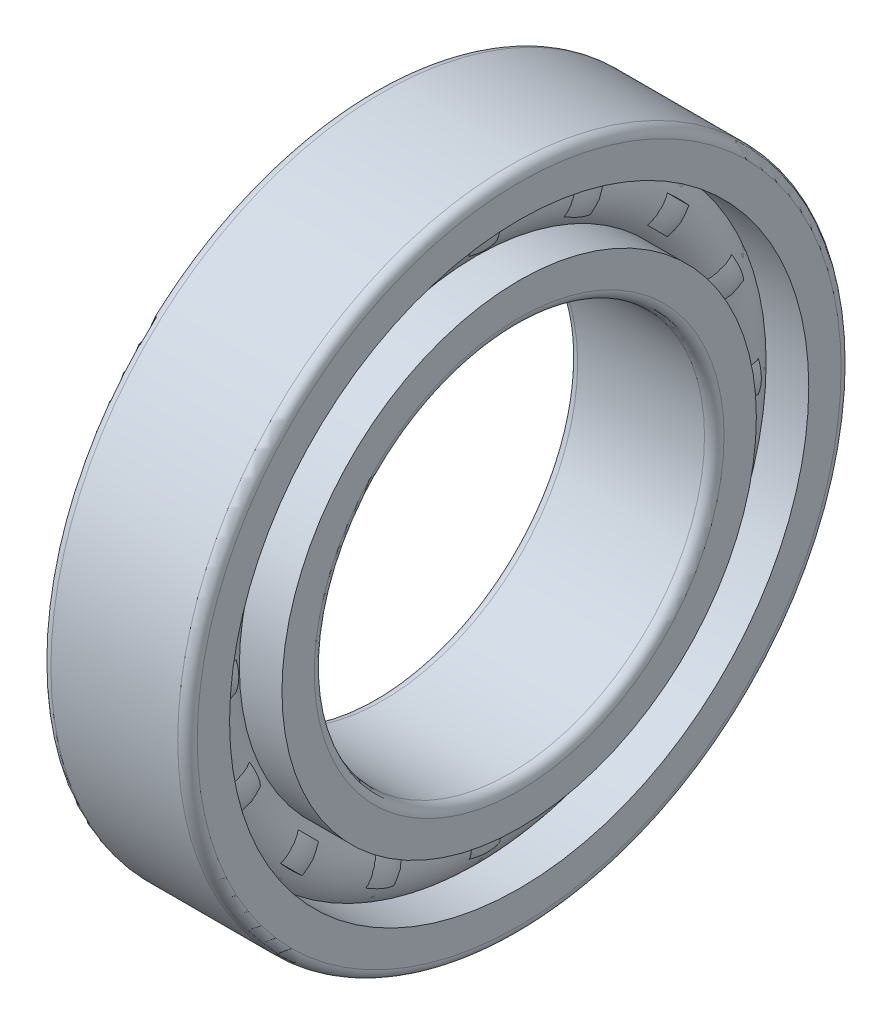
SolidWorks part; units mm, degrees
ref_plane "Přední rovina" through (0, 0, 0) normal (0, 0, 1) x (1, 0, 0)
ref_plane "Vrchní rovina" through (0, 0, 0) normal (0, 1, 0) x (1, 0, 0)
ref_plane "Pravá rovina" through (0, 0, 0) normal (1, 0, 0) x (0, 0, -1)
sketch "Skica1" plane through (0, 0, 0) normal (0, 0, 1) x (1, 0, 0)
  line L0 (0, 20) -> (0, 0) construction
  line L1 (-7.5, 34) -> (7.5, 34)
  line L2 (-7.5, 34) -> (-7.5, 20)
  line L3 (-7.5, 20) -> (7.5, 20)
  line L4 (7.5, 34) -> (7.5, 20)
  line L5 (0, 0) -> (7.5, 0) construction
  dimension "B" = 15
  dimension "d" = 40
  dimension "D_" = 68
sketch "Skica2" plane through (0, 0, 0) normal (0, 0, 1) x (1, 0, 0)
  line L0 (7.5, 34) -> (7.5, 20) construction
  line L1 (-7.5, 34) -> (7.5, 34)
  line L2 (-7.5, 34) -> (-7.5, 29.6859)
  line L3 (-7.5, 29.6859) -> (-3.1293, 29.6859)
  line L4 (7.5, 34) -> (7.5, 29.6859)
  line L5 (-7.5, 34) -> (-7.5, 20) construction
  line L6 (7.5, 20) -> (-7.5, 20)
  line L7 (7.5, 20) -> (7.5, 24.3141)
  line L8 (7.5, 24.3141) -> (3.1293, 24.3141)
  line L9 (-7.5, 20) -> (-7.5, 24.3141)
  line L10 (7.5, 29.6859) -> (4.1239, 27) construction
  line L11 (7.5, 29.6859) -> (-7.5, 24.3141) construction
  line L12 (0, 29.6859) -> (0, 31.1239) construction
  line L14 (3.1293, 29.6859) -> (7.5, 29.6859)
  line L15 (-3.1293, 24.3141) -> (-7.5, 24.3141)
  line L16 (0, 0) -> (-7.5, 0) construction
  line L17 (0, 27) -> (0, 22.8761) construction
  line L18 (0, 31.1239) -> (0, 32.562) construction
  line L19 (0, 32.562) -> (0, 34) construction
  circle A0 centre (0, 27) radius 4.1239 construction
  arc A1 (-3.1293, 29.6859) -> (3.1293, 29.6859) centre (0, 27) cw
  arc A2 (-3.1293, 24.3141) -> (3.1293, 24.3141) centre (0, 27) ccw
revolve "Otočit kolem osy1" add sketch "Skica2" angle 360 about L16
fillet "Zaoblit1" radius 1 2 edges at (7.5, 0, -34) (-7.5, 0, -34)
fillet "Zaoblit2" radius 1 2 edges at (7.5, 0, -20) (-7.5, 0, -20)
sketch "Skica3" plane through (0, 0, 0) normal (0, 0, 1) x (1, 0, 0)
  line L0 (0, 0) -> (7.5, 0) construction
  line L1 (7.5, -33) -> (7.5, 33) construction
  circle A0 centre (0, 27) radius 4.1239
  arc A1 (3.1293, 29.6859) -> (-3.1293, 29.6859) centre (0, 27) ccw construction
  circle A2 centre (0, 27) radius 4.1139
  dimension "D1" = 0.01
revolve "Otočit kolem osy2" add sketch "Skica3" angle 360 about L0
sketch "Skica5" plane through (0, 0, 0) normal (0, 0, -1) x (1, 0, 0)
  line L0 (0, -22.8761) -> (0, -31.1239) construction
  arc A0 (0, -31.1239) -> (0, -22.8761) centre (0, -27) ccw
  arc A3 (-3.1293, -29.6859) -> (3.1293, -29.6859) centre (0, -27) ccw construction
surface "Povrch-Otočit kolem osy3" sketch "Skica5" parameters "D1"=360
pattern_circular "Kruhové pole1" count 16 over 360 about axis through (0, 0, 0) along (1, 0, 0) of bodies 108
sketch "Skica6" plane through (0, 0, 0) normal (1, 0, 0) x (0, 0, -1)
  line L4 (0, 31.1239) -> (0, 28.3746) construction
  line L5 (0, 22.8761) -> (0, 25.6254) construction
  line L6 (0, 25.6254) -> (0, 28.3746) construction
  line L7 (3.976, 28.0947) -> (4.2768, 28.0505)
  line L8 (3.7774, 25.3454) -> (4.0631, 25.3012)
  line L9 (0, 24.3141) -> (0, 22.8761) construction
  arc A0 (3.7774, 25.3454) -> (3.976, 28.0947) centre (0, 27) ccw
  arc A1 (4.0631, 25.3012) -> (4.2768, 28.0505) centre (0, 27) ccw
  circle A2 centre (0, 0) radius 25.6254 construction
  circle A3 centre (0, 0) radius 28.3746 construction
  circle A4 centre (0, 27) radius 4.1239 construction
  dimension "D1" = 0.28
surface "Povrch-Otočit kolem osy4" sketch "Skica6" parameters "D1"=360
pattern_circular "Kruhové pole3" count 16 over 360 about axis through (0, 0, 0) along (1, 0, 0) of bodies 128
ref_plane "Rovina1" through (0, 0, 0) normal (0, -0.1951, 0.9808) x (1, 0, 0)
sketch "Skica7" plane through (0, 0, 0) normal (0, -0.1951, 0.9808) x (1, 0, 0)
  line L0 (0, 28.3746) -> (0, 25.6254) construction
  line L1 (-0.56, 28.0946) -> (0.56, 28.0946)
  line L2 (-0.56, 28.0946) -> (-0.56, 25.9054)
  line L3 (-0.56, 25.9054) -> (0.56, 25.9054)
  line L4 (0.56, 28.0946) -> (0.56, 25.9054)
  line L9 (0, 28.3746) -> (0, 28.0946) construction
  line L10 (0, 25.6254) -> (0, 25.9054) construction
  dimension "D1" = 0.28
  dimension "D2" = 1.12
surface "Povrch-Vysunout1" sketch "Skica7"
mirror "Zrcadlit1" about plane through (0, 0, 0) normal (0, -0.1951, 0.9808) of bodies 504
surface "Povrch-Sešít1"
pattern_circular "Kruhové pole4" count 16 over 360 about axis through (0, 0, 0) along (1, 0, 0) of bodies 530
equation "\"D1@Zaoblit1\" = \"rs@Zaoblit2\""
equation "\"D1@Skica6\" = (\"D_@Skica1\"-\"d@Skica1\")/100"
equation "\"D1@Kruhové pole3\" = \"n@Kruhové pole1\""
equation "\"D1@Rovina1\" =180/\"D1@Kruhové pole3\""
equation "\"D2@Skica7\" = \"D1@Skica6\" * 4"
equation "\"D1@Skica7\" = \"D2@Skica7\" / 4"
equation "\"D1@Kruhové pole4\" = \"D1@Kruhové pole3\""
